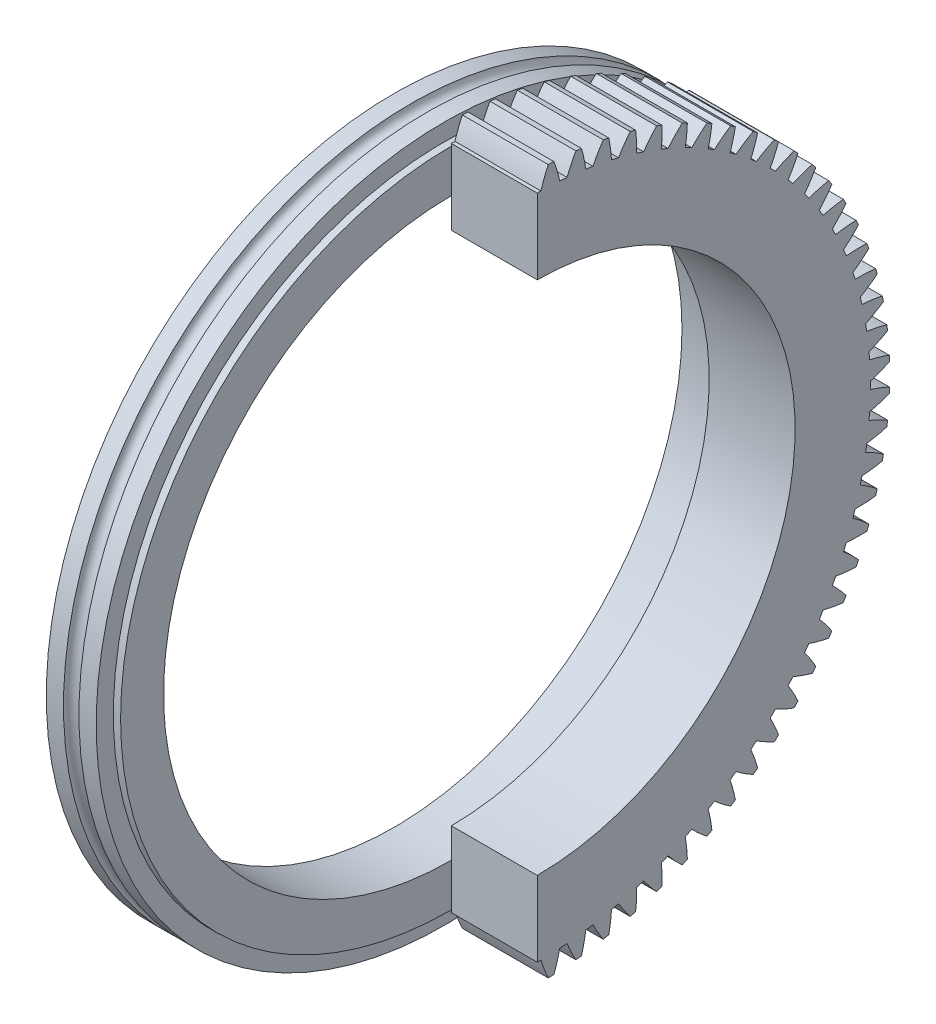
SolidWorks part; units mm, degrees
ref_plane "Plane1" through (0, 0, 0) normal (0, 0, 1) x (1, 0, 0)
ref_plane "Plane2" through (0, 0, 0) normal (0, 1, 0) x (1, 0, 0)
ref_plane "Plane3" through (0, 0, 0) normal (1, 0, 0) x (0, 0, -1)
sketch "HoldingSke" plane through (0, 0, 0) normal (0, 1, 0) x (1, 0, 0)
  line L0 (0, 0) -> (44.1066, -250.1412)
  line L1 (-15, 0) -> (100, 0) construction
  line L2 (0, 0) -> (-2.1039, 2.3779)
  line L3 (0, 0) -> (-11.863, 4.5341)
  line L4 (0, 0) -> (1.4996, 8.5048)
  line L5 (0, 0) -> (-47.5972, -17.7524)
  line L6 (0, 0) -> (-21.0557, -14.2063)
  line L7 (-2.1039, 2.3779) -> (8.8308, 51.9871)
  line L8 (-76.2, 54.61) -> (-75.184, 54.61)
  line L9 (-71.009, 38.7566) -> (-53.1078, 45.2721)
  line L10 (-76.2, 71.12) -> (104.1128, 71.12)
  line L11 (0, 0) -> (-25.4, 0)
  line L12 (-76.2, 101.6) -> (-76.0984, 101.6)
  line L13 (24.9733, 27.94) -> (52.9518, 28.4284)
  line L14 (24.9733, 27.94) -> (24.9746, 27.94)
  line L15 (24.9733, 27.94) -> (100.4006, 29.5858)
  circle A0 centre (0, 0) radius 0.3969
  circle A1 centre (0, 0) radius 38.1
  circle A2 centre (0, 0) radius 38.1
  circle A3 centre (0, 0) radius 0.3969
  dimension "MHD" = 76.2
  dimension "Hub_dia" = 76.2
  dimension "Bore" = 0.7937
  dimension "MBD" = 0.7937
  dimension "Num_teeth" = 80
  dimension "Pitch" = 254
  dimension "Overall_len" = 50.8
  dimension "Show_teeth" = 80
  dimension "Thickness" = 25.4
  dimension "OAL" = 50.8001
  dimension "T_dim" = 1.016
  dimension "Ap" = 20
  dimension "H" = 19.05
  dimension "Pitch_radius" = 180.3128
  dimension "Width" = 25.4
  dimension "Backlash" = 0.1016
  dimension "Addendum_fac" = 1
  dimension "Dedendum_fac" = 1.25
  dimension "Clearance_fac" = 0.25
  dimension "Dedendum_add" = 0.0013
sketch "BasProSke" plane through (0, 0, 0) normal (0, 1, 0) x (1, 0, 0)
  line L0 (-10, 0) -> (60, 0) construction
  line L1 (0, 0) -> (0, 104.14)
  line L2 (0, 0) -> (25.4, 0)
  line L3 (25.4, 0) -> (25.4, 104.14)
  line L4 (25.4, 104.14) -> (0, 104.14)
  dimension "Thickness" = 25.4
  dimension "Diameter" = 208.28
revolve "Base-Revolve" add sketch "BasProSke" angle 360 about L0
sketch "TooCutSke" plane through (0, 0, 0) normal (1, 0, 0) x (0, 0, -1)
  line L1 (0, 0) -> (0, 107) construction
  line L2 (0, 0) -> (-2.1726, 101.5768) construction
  line L3 (0, 0) -> (-7.9763, 203.0109) construction
  line L4 (-2.1726, 101.5768) -> (-3.9882, 101.5054) construction
  arc A0 (1.0772, 98.4178) -> (-1.0772, 98.4178) centre (0, 0) ccw
  arc A1 (3.2722, 104.114) -> (-3.2722, 104.114) centre (0, 0) ccw
  circle A2 centre (0, 0) radius 101.6 construction
  circle A3 centre (0, 0) radius 95.4728 construction
  arc A4 (-1.0772, 98.4178) -> (-3.2722, 104.114) centre (-39.9895, 86.6942) ccw
  arc A5 (3.2722, 104.114) -> (1.0772, 98.4178) centre (39.9895, 86.6942) ccw
  dimension "Root_dia" = 196.8475
  dimension "Overcut_dia" = 208.3308
  dimension "Pitch_dia" = 203.2
  dimension "Base_dia" = 190.9455
  dimension "Flank_rad" = 40.64
  dimension "Half_ang" = 2.25
  dimension "Half_CT" = 1.817
extrude "ToothCut" cut sketch "TooCutSke" along normal through all
fillet "Breaks" [suppressed] radius 0.0508
fillet "RootFillets" [suppressed] radius 0.6363
pattern_circular "TeethCuts" count 80 every 4.5 about axis through (-10, 0, 0) along (1, 0, 0) of "ToothCut", "RootFillets", "Breaks"
sketch "HubNeaOneSke" plane through (0, 0, 0) normal (-1, 0, 0) x (0, 0, 1)
  circle A0 centre (0, 0) radius 38.1
  dimension "Diameter" = 76.2
extrude "HubNearOne" [suppressed] add sketch "HubNeaOneSke" along normal blind 25.4001
sketch "HubNeaBotSke" plane through (0, 0, 0) normal (-1, 0, 0) x (0, 0, 1)
  circle A0 centre (0, 0) radius 38.1
  dimension "Diameter" = 76.2
extrude "HubNearBoth" [suppressed] add sketch "HubNeaBotSke" along normal blind 12.7
ref_plane "FarPln" through (25.4, 0, 0) normal (1, 0, 0) x (0, 0, -1)
sketch "HubFarSke" plane through (25.4, 0, 0) normal (1, 0, 0) x (0, 0, -1)
  circle A0 centre (0, 0) radius 38.1
  dimension "Diameter" = 76.2
extrude "HubFar" [suppressed] add sketch "HubFarSke" along normal blind 12.7
sketch "BorSke" plane through (0, 0, 0) normal (1, 0, 0) x (0, 0, -1)
  circle A0 centre (0, 0) radius 0.3969
  dimension "Diameter" = 0.7937
extrude "Bore" cut sketch "BorSke" along normal mid plane 101.6001
sketch "KeySke" plane through (0, 0, 0) normal (1, 0, 0) x (0, 0, -1)
  line L0 (-0.127, 0) -> (-0.127, 0.6191)
  line L1 (-0.127, 0.6191) -> (0.127, 0.6191)
  line L2 (0.127, 0.6191) -> (0.127, 0)
  line L3 (0, 0) -> (0, 34) construction
  line L4 (-0.127, 0) -> (0.127, 0)
  dimension "Offset" = 0.6191
  dimension "Width" = 0.254
extrude "Keyway" [suppressed] cut sketch "KeySke" along normal mid plane 101.6001
pattern_circular "Keyway2" [suppressed] count 2 every 90 about axis through (-10, 0, 0) along (1, 0, 0)
sketch "Sketch1" plane through (25.4, 0, 0) normal (1, 0, 0) x (0, 0, -1)
  circle A0 centre (0, 0) radius 76.2
  dimension "D1" = 152.4
extrude "Cut-Extrude1" cut sketch "Sketch1" against normal up to next
sketch "Sketch2" plane through (25.4, 0, 0) normal (1, 0, 0) x (0, 0, -1)
  line L0 (0, -122.362) -> (0, 129.1599)
  line L1 (0, 129.1599) -> (-138.5323, 129.1599)
  line L2 (-138.5323, 129.1599) -> (-138.5323, -122.362)
  line L3 (-138.5323, -122.362) -> (0, -122.362)
extrude "Cut-Extrude2" cut sketch "Sketch2" against normal up to next
sketch "Sketch4" plane through (0, 0, 0) normal (0, 1, 0) x (1, 0, 0)
  line L0 (0, 97.739) -> (-2.1405, 97.739)
  line L1 (-2.1405, 97.739) -> (-2.1405, 102.819)
  line L2 (-2.1405, 102.819) -> (-7.2205, 102.819)
  line L3 (-11.7925, 102.819) -> (-16.8725, 102.819)
  line L4 (-16.8725, 102.819) -> (-16.8725, 97.739)
  line L5 (-16.8725, 93.167) -> (-16.8725, 85.039)
  line L9 (0, 0) -> (-16.8725, 0) construction
  line L12 (-16.8725, 85.039) -> (0, 85.039)
  line L13 (0, 90.4539) -> (0, 84.4778) construction
  line L14 (0, 85.039) -> (0, 97.739)
  line L15 (25.4, 104.089) -> (0, 104.089) construction
  arc A0 (-7.2205, 102.819) -> (-11.7925, 102.819) centre (-9.5065, 102.819) cw
  arc A1 (-16.8725, 97.739) -> (-16.8725, 93.167) centre (-16.8725, 95.453) cw
  dimension "D1" = 2.286
  dimension "D2" = 2.286
  dimension "D3" = 5.08
  dimension "D4" = 5.08
  dimension "D5" = 12.7
  dimension "D6" = 6.35
revolve "Revolve1" add sketch "Sketch4" angle 360 about L9
equation "' \"Pitch@HoldingSke\" = 4"
equation "' \"Num_teeth@HoldingSke\" = 12"
equation "' \"Ap@HoldingSke\" =  20"
equation "' \"Ap@HoldingSke\" = 20"
equation "' \"Width@HoldingSke\" = 0.5"
equation "' \"Hub_dia@HoldingSke\"= 1"
equation "' \"Hub_dia@HoldingSke\" = 1"
equation "' \"Overall_len@HoldingSke\" = 1.0"
equation "' \"Bore@HoldingSke\" = 0.75"
equation "' \"T_dim@HoldingSke\" = 0.85"
equation "' \"Width@KeySke\" = 0.25"
equation "' \"Show_teeth@HoldingSke\" = 13"
equation "' \"Backlash@HoldingSke\" = 0.009"
equation "' \"Addendum_fac@HoldingSke\" = 1.0"
equation "' \"Dedendum_fac@HoldingSke\" = 1.25"
equation "' \"Dedendum_add@HoldingSke\" = 0.00005"
equation "' \"Clearance_fac@HoldingSke\" = 0.25"
equation "' \"Pitch@HoldingSke\" = 0.5"
equation "' \"Num_teeth@HoldingSke\" = 23"
equation "' \"Show_teeth@HoldingSke\" = 23"
equation "' \"Backlash@HoldingSke\" = 0.0375"
equation "\"Overcut_dia@TooCutSke\" = (\"Num_teeth@HoldingSke\" + 2 * \"Addendum_fac@HoldingSke\") / \"Pitch@HoldingSke\" + 0.002"
equation "\"Pitch_dia@TooCutSke\" = \"Num_teeth@HoldingSke\" / \"Pitch@HoldingSke\""
equation "\"Base_dia@TooCutSke\" = \"Num_teeth@HoldingSke\" / \"Pitch@HoldingSke\" * cos((\"Ap@HoldingSke\"  * 3.14159265 / 180))"
equation "\"Root_dia@TooCutSke\" = (\"Num_teeth@HoldingSke\" + 2) / \"Pitch@HoldingSke\" - 2 * (\"Addendum_fac@HoldingSke\" + \"Dedendum_fac@HoldingSke\") / \"Pitch@HoldingSke\" - \"Dedendum_add@HoldingSke\" * 2"
equation "\"Half_ang@TooCutSke\" = 180 / \"Num_teeth@HoldingSke\""
equation "\"Half_CT@TooCutSke\" = \"Num_teeth@HoldingSke\" / \"Pitch@HoldingSke\" * sin((3.14159265 / 2 / \"Num_teeth@HoldingSke\")) / 2 - 7 * \"Backlash@HoldingSke\" / 4"
equation "\"Flank_rad@TooCutSke\" = \"Num_teeth@HoldingSke\" / \"Pitch@HoldingSke\" / 5"
equation "\"Radius@RootFillets\" = \"Clearance_fac@HoldingSke\" / \"Pitch@HoldingSke\" + \"Dedendum_add@HoldingSke\""
equation "\"Break_rad@Breaks\" = 0.02 / \"Pitch@HoldingSke\""
equation "\"Thickness@HoldingSke\" = \"Width@HoldingSke\""
equation "\"OAL@HoldingSke\" = \"Thickness@HoldingSke\""
equation "\"MHD@HoldingSke\" = (\"Num_teeth@HoldingSke\" + 2) / \"Pitch@HoldingSke\" - 2 * (\"Addendum_fac@HoldingSke\" + \"Dedendum_fac@HoldingSke\")  / \"Pitch@HoldingSke\" - \"Dedendum_add@HoldingSke\" * 2"
equation "\"MBD@HoldingSke\" = (\"Num_teeth@HoldingSke\" + 2) / \"Pitch@HoldingSke\" - 2 * (\"Addendum_fac@HoldingSke\" + \"Dedendum_fac@HoldingSke\")  / \"Pitch@HoldingSke\" - \"Dedendum_add@HoldingSke\" * 2 - 0.002"
equation "\"MHD@HoldingSke\" = ((sgn( \"MHD@HoldingSke\" - \"Hub_dia@HoldingSke\" )-1)*( \"MHD@HoldingSke\" - \"Hub_dia@HoldingSke\" ))/-2+ \"Hub_dia@HoldingSke\""
equation "\"MBD@HoldingSke\" = ((sgn( \"MBD@HoldingSke\" - \"Bore@HoldingSke\" )-1)*( \"MBD@HoldingSke\" - \"Bore@HoldingSke\" ))/-2+ \"Bore@HoldingSke\""
equation "\"OAL@HoldingSke\" = ((sgn( \"OAL@HoldingSke\" - \"Overall_len@HoldingSke\" )+1)*( \"OAL@HoldingSke\" - \"Overall_len@HoldingSke\" ))/2 + \"Overall_len@HoldingSke\" + 0.000002"
equation "\"Num_teeth@TeethCuts\" = int( \"Show_teeth@HoldingSke\" ) + 1"
equation "\"Num_teeth@TeethCuts\" = ((sgn( \"Num_teeth@TeethCuts\" - \"Num_teeth@HoldingSke\" )-1)*( \"Num_teeth@TeethCuts\" - \"Num_teeth@HoldingSke\" ))/-2+ \"Num_teeth@HoldingSke\""
equation "\"Num_teeth@TeethCuts\" = ((sgn( \"Num_teeth@TeethCuts\" - 2.0)+1)*( \"Num_teeth@TeethCuts\" - 2.0))/2 +2.0"
equation "\"Angle@TeethCuts\" = 360.0 / \"Num_teeth@HoldingSke\""
equation "\"Diameter@BasProSke\" = (\"Num_teeth@HoldingSke\" + 2 * \"Addendum_fac@HoldingSke\") / \"Pitch@HoldingSke\""
equation "\"Thickness@BasProSke\"  = \"Thickness@HoldingSke\""
equation "' \"Fillet_rad@BasProSke\" =  \"Thickness@HoldingSke\" * 0.05"
equation "' \"Fillet_rad@BasProSke\" = \"Thickness@HoldingSke\" * 0.05"
equation "\"MHD@HoldingSke\" = ((sgn( \"MHD@HoldingSke\" - \"Root_dia@TooCutSke\" )-1)*( \"MHD@HoldingSke\" - \"Root_dia@TooCutSke\" ))/-2+ \"Root_dia@TooCutSke\""
equation "\"Diameter@HubNeaOneSke\" = \"MHD@HoldingSke\""
equation "\"Length@HubNearOne\" = \"OAL@HoldingSke\" - \"Thickness@BasProSke\""
equation "\"Diameter@HubNeaBotSke\" = \"MHD@HoldingSke\""
equation "\"Length@HubNearBoth\" = ( \"OAL@HoldingSke\" - \"Thickness@BasProSke\" ) / 2.0"
equation "\"Thickness@FarPln\" = \"Thickness@BasProSke\""
equation "\"Diameter@HubFarSke\" = \"MHD@HoldingSke\""
equation "\"Length@HubFar\" = ( \"OAL@HoldingSke\" - \"Thickness@BasProSke\" ) / 2.0"
equation "\"Diameter@BorSke\" = \"MBD@HoldingSke\""
equation "\"D1@Bore\" = \"OAL@HoldingSke\" * 2.0"
equation "\"D1@Keyway\" = \"OAL@HoldingSke\" * 2.0"
equation "\"Offset@KeySke\" = \"T_dim@HoldingSke\" - \"MBD@HoldingSke\" / 2.0"
